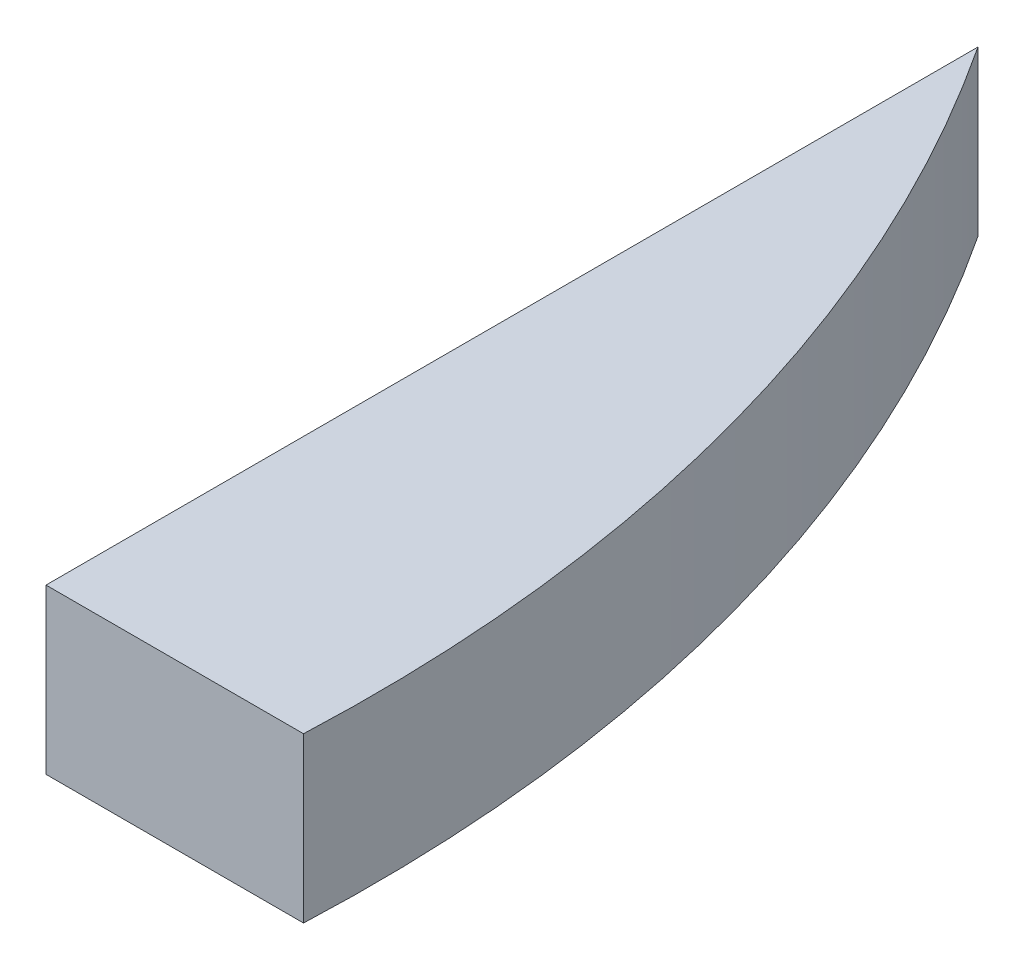
SolidWorks part; units mm, degrees
material "Rubber"
ref_plane "Front Plane" through (0, 0, 0) normal (0, 0, 1) x (1, 0, 0)
ref_plane "Top Plane" through (0, 0, 0) normal (0, 1, 0) x (1, 0, 0)
ref_plane "Right Plane" through (0, 0, 0) normal (1, 0, 0) x (0, 0, -1)
ref_plane "Plane1" through (0, -25.8, 0) normal (0, -1, 0) x (1, 0, 0)
sketch "Sketch1" plane through (0, -25.8, 0) normal (0, -1, 0) x (1, 0, 0)
  line L0 (0, -142.57) -> (0, -146.6697)
  line L47 (0, 0) -> (0, -142.57)
  line L48 (40.5244, 0) -> (0, 0)
  arc A20 (0, -146.6697) -> (34.2419, -67.0211) centre (-206.6759, -10.6324) ccw
  arc A24 (34.2419, -67.0211) -> (40.5244, 0) centre (-206.6759, -10.6324) ccw
  point P1 (0, 0)
  dimension "D1" = 142.57
extrude "Boss-Extrude1" add sketch "Sketch1" against normal blind 25.8
